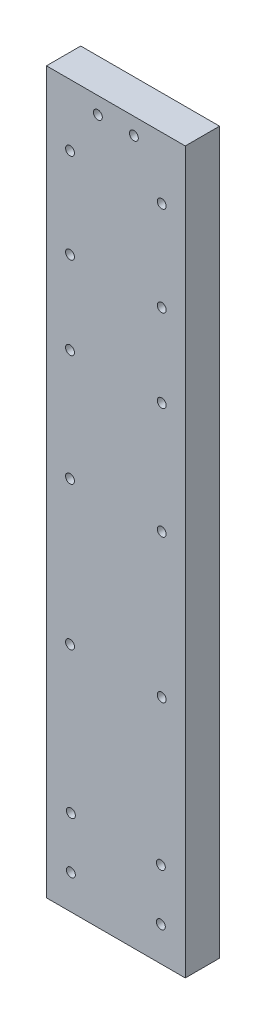
SolidWorks part; units mm, degrees
ref_plane "Front Plane" through (0, 0, 0) normal (0, 0, 1) x (1, 0, 0)
ref_plane "Top Plane" through (0, 0, 0) normal (0, 1, 0) x (1, 0, 0)
ref_plane "Right Plane" through (0, 0, 0) normal (1, 0, 0) x (0, 0, -1)
sketch "Sketch1" plane through (0, 0, 0) normal (0, 0, 1) x (1, 0, 0)
  line L0 (0, 0) -> (0, 84.09)
  line L1 (16.2, 0) -> (16.2, 84.09)
  line L2 (0, 46.24) -> (16.2, 46.24) construction
  line L3 (0, 0) -> (16.2, 0)
  line L4 (0, 12.5) -> (16.2, 12.5) construction
  line L5 (0, 24.5) -> (16.2, 24.5) construction
  line L6 (16.2, 84.09) -> (0, 84.09)
  line L7 (0, 68.885) -> (16.2, 68.885) construction
  line L8 (0, 54.24) -> (16.2, 54.24) construction
  line L10 (0, 74.885) -> (16.2, 74.885) construction
  circle A0 centre (13.45, 43.74) radius 0.52
  circle A1 centre (2.75, 66.385) radius 0.52
  circle A2 centre (13.45, 56.74) radius 0.52
  circle A3 centre (13.45, 76.885) radius 0.52
  circle A4 centre (2.75, 27) radius 0.52
  circle A5 centre (2.75, 76.885) radius 0.52
  circle A6 centre (2.75, 56.74) radius 0.52
  circle A7 centre (2.85, 10) radius 0.52
  circle A8 centre (13.35, 10) radius 0.52
  circle A9 centre (13.35, 4) radius 0.52
  circle A10 centre (2.85, 4) radius 0.52
  circle A11 centre (6, 82.135) radius 0.52
  circle A12 centre (13.45, 27) radius 0.52
  circle A13 centre (13.45, 66.385) radius 0.52
  circle A14 centre (10.2, 82.135) radius 0.52
  circle A15 centre (2.75, 43.74) radius 0.52
  dimension "D1" = 4
  dimension "D2" = 4
  dimension "D3" = 6
  dimension "D4" = 6
  dimension "D5" = 2.5
  dimension "D6" = 12
  dimension "D7" = 2.85
  dimension "D8" = 2.85
  dimension "D9" = 2.85
  dimension "D10" = 16.2
  dimension "D11" = 21.74
  dimension "D12" = 2.75
  dimension "D13" = 2.75
  dimension "D14" = 2.75
  dimension "D15" = 2.75
  dimension "D16" = 2.5
  dimension "D17" = 2.5
  dimension "D18" = 2.5
  dimension "D19" = 2.5
  dimension "D20" = 8
  dimension "D21" = 14.645
  dimension "D22" = 2.75
  dimension "D23" = 2.75
  dimension "D24" = 2.5
  dimension "D25" = 2.5
  dimension "D26" = 2.5
  dimension "D27" = 2.5
  dimension "D28" = 2.75
  dimension "D29" = 2.75
  dimension "D30" = 6
  dimension "D31" = 9.205
  dimension "D32" = 2.75
  dimension "D33" = 6
  dimension "D34" = 2
  dimension "D35" = 7.25
  dimension "D36" = 2
  dimension "D37" = 7.25
  dimension "D38" = 6
  dimension "D39" = 2.75
extrude "Boss-Extrude1" add sketch "Sketch1" along normal blind 4
equation "\"D11@Sketch1\"= \"HL@parametersSketch@prostheticParameters.SLDPRT\" * 0.204 - 4 - 12 'Pinky PIP Length"
equation "\"D21@Sketch1\"= \"HL@parametersSketch@prostheticParameters.SLDPRT\" * 0.117 - 4 - 3 'Pinky MIP Length"
equation "\"D31@Sketch1\"= \"HL@parametersSketch@prostheticParameters.SLDPRT\" * 0.093 - 3 - 5'Pinky DIP Length"
equation "\"D10@Sketch1\"= \"fingerWidth@parametersSketch@prostheticParameters.SLDPRT\"'Pinky Width"
